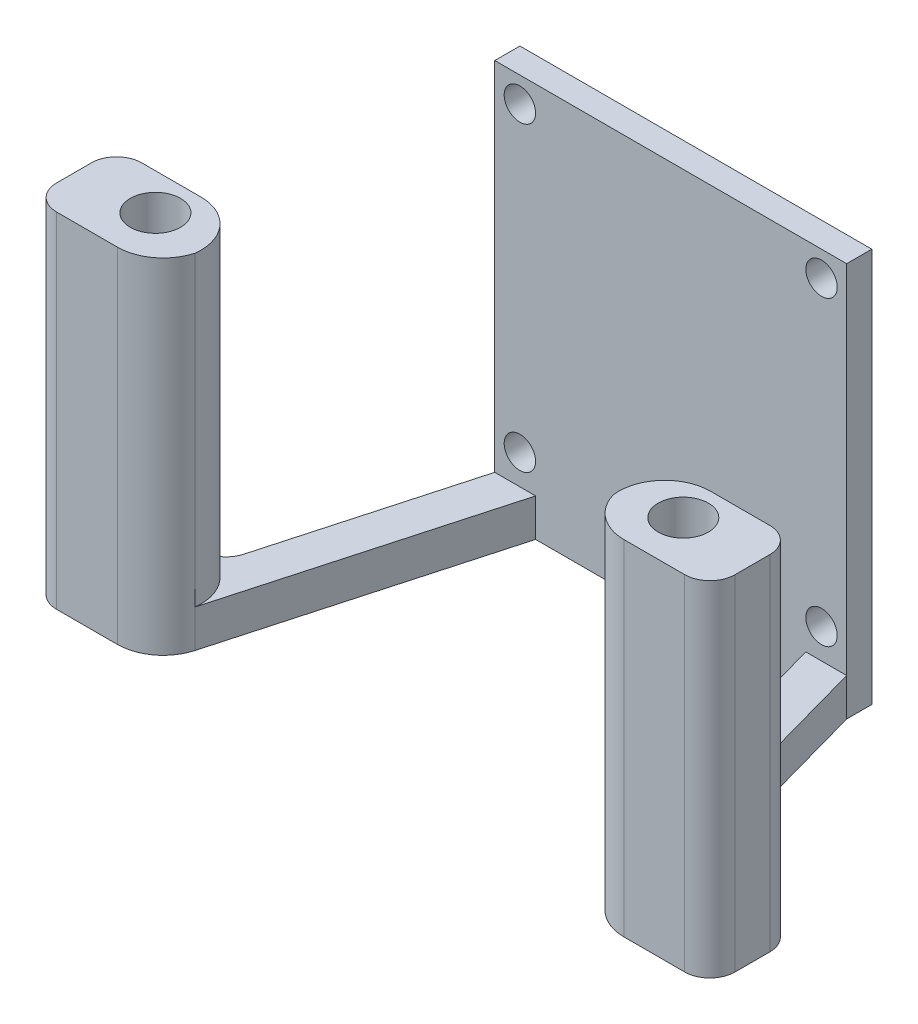
SolidWorks part; units mm, degrees
ref_plane "前视基准面" through (0, 0, 0) normal (0, 0, 1) x (1, 0, 0)
ref_plane "上视基准面" through (0, 0, 0) normal (0, 1, 0) x (1, 0, 0)
ref_plane "右视基准面" through (0, 0, 0) normal (1, 0, 0) x (0, 0, -1)
sketch "草图1" plane through (0, 0, 0) normal (0, 0, 1) x (1, 0, 0)
  line L0 (-14, 14) -> (-14, -17.3762)
  line L1 (-14, -17.3762) -> (14, -17.3762)
  line L2 (14, -17.3762) -> (14, 14)
  line L3 (14, 14) -> (-14, 14)
  circle A0 centre (-12, -12) radius 1.25
  circle A1 centre (-12, 12) radius 1.25
  circle A2 centre (12, 12) radius 1.25
  circle A3 centre (12, -12) radius 1.25
extrude "凸台-拉伸1" add sketch "草图1" along normal blind 4
ref_plane "基准面1" through (0, -17.3762, 0) normal (0, 1, 0) x (1, 0, 0)
sketch "草图4" plane through (0, -17.3762, 0) normal (0, 1, 0) x (1, 0, 0)
  line L4 (-10.75, -4) -> (-16.6423, -25.199)
  line L5 (-10.75, -4) -> (-14, -4)
  line L6 (-20.1398, -27.8735) -> (-24.9913, -27.8735)
  line L7 (-26.9913, -25.8735) -> (-26.9913, -23.0981)
  line L8 (-14, -4) -> (-18.3454, -19.6337)
  line L9 (-20.2724, -21.0981) -> (-24.9913, -21.0981)
  circle A0 centre (-21, -24) radius 2
  arc A1 (-16.6423, -25.199) -> (-20.1398, -27.8735) centre (-20.1617, -24.2208) cw
  arc A2 (-18.3454, -19.6337) -> (-20.2724, -21.0981) centre (-20.2724, -19.0981) cw
  arc A3 (-26.9913, -23.0981) -> (-24.9913, -21.0981) centre (-24.9913, -23.0981) cw
  arc A4 (-26.9913, -25.8735) -> (-24.9913, -27.8735) centre (-24.9913, -25.8735) ccw
  dimension "D3" = 4
  dimension "D4" = 2
extrude "凸台-拉伸3" add sketch "草图4" along normal blind 3
sketch "草图5" plane through (0, -14.3762, 0) normal (0, 1, 0) x (1, 0, 0)
  line L0 (0, -4) -> (0, -31.9873)
  line L1 (14, -4) -> (-14, -4) construction
sketch "草图6" plane through (0, -14.3762, 0) normal (0, 1, 0) x (1, 0, 0)
  line L6 (-14, -4) -> (-18.3454, -19.6337)
  line L7 (-20.2724, -21.0981) -> (-24.9913, -21.0981)
  line L8 (-26.9913, -23.0981) -> (-26.9913, -25.8735)
  line L9 (-24.9913, -27.8735) -> (-20.1398, -27.8735)
  line L10 (-16.6423, -25.199) -> (-10.75, -4)
  line L11 (-10.75, -4) -> (-14, -4)
  line L13 (-20.2724, -21.0981) -> (-24.9913, -21.0981)
  line L14 (-26.9913, -23.0981) -> (-26.9913, -25.8735)
  line L15 (-24.9913, -27.8735) -> (-20.1398, -27.8735)
  line L17 (-10.75, -4) -> (-14, -4)
  arc A0 (-20.2724, -21.0981) -> (-16.6423, -25.199) centre (-20.2724, -24.7552) cw
  arc A4 (-20.2724, -21.0981) -> (-18.3454, -19.6337) centre (-20.2724, -19.0981) ccw
  arc A5 (-24.9913, -21.0981) -> (-26.9913, -23.0981) centre (-24.9913, -23.0981) ccw
  arc A6 (-26.9913, -25.8735) -> (-24.9913, -27.8735) centre (-24.9913, -25.8735) ccw
  arc A7 (-20.1398, -27.8735) -> (-16.6423, -25.199) centre (-20.1617, -24.2208) ccw
  arc A9 (-24.9913, -21.0981) -> (-26.9913, -23.0981) centre (-24.9913, -23.0981) ccw
  arc A10 (-26.9913, -25.8735) -> (-24.9913, -27.8735) centre (-24.9913, -25.8735) ccw
  arc A11 (-20.1398, -27.8735) -> (-16.6423, -25.199) centre (-20.1617, -24.2208) ccw
  line M13 (-20.2724, -21.0981) -> (-24.9913, -21.0981)
  arc M14 (-24.9913, -21.0981) -> (-26.9913, -23.0981) centre (-24.9913, -23.0981) ccw
  line M15 (-26.9913, -23.0981) -> (-26.9913, -25.8735)
  arc M16 (-26.9913, -25.8735) -> (-24.9913, -27.8735) centre (-24.9913, -25.8735) ccw
  line M17 (-24.9913, -27.8735) -> (-20.1398, -27.8735)
  arc M18 (-20.1398, -27.8735) -> (-16.6423, -25.199) centre (-20.1617, -24.2208) ccw
  circle M21 centre (-21, -24) radius 2
  dimension "D1" = 0
extrude "凸台-拉伸4" add sketch "草图6" along normal blind 24.38 contours A0 M13 M14 M15 M16 M17 M18 M21
mirror "镜向1" about plane through (0, 0, 0) normal (1, 0, 0) of "凸台-拉伸4", "凸台-拉伸3"
sketch "草图7" plane through (0, 14, 0) normal (0, 1, 0) x (1, 0, 0)
  line L0 (-14, -2) -> (14, -2)
  line L4 (14, 0) -> (-14, 0)
  line L5 (-14, 0) -> (-14, -4)
  line L6 (-14, -4) -> (14, -4)
  line L7 (14, -4) -> (14, 0)
  line L8 (14, 0) -> (-14, 0)
  line L9 (-14, 0) -> (-14, -4)
  line L10 (-14, -4) -> (14, -4)
  line L11 (14, -4) -> (14, 0)
  line M5 (14, 0) -> (-14, 0)
  line M6 (-14, 0) -> (-14, -4)
  line M8 (14, -4) -> (14, 0)
  dimension "D1" = 0
extrude "切除-拉伸1" cut sketch "草图7" against normal blind 72 contours L0 M6 M8 M5
